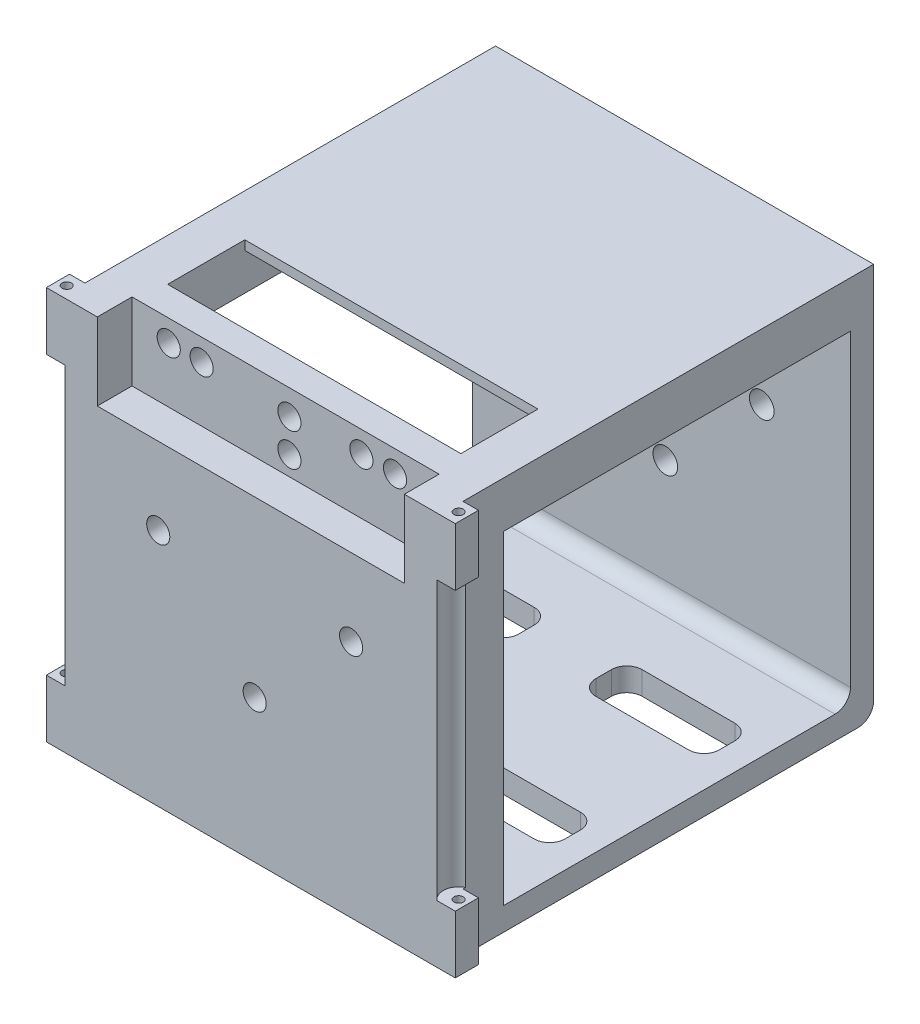
SolidWorks part; units mm, degrees
ref_plane "前视基准面" through (0, 0, 0) normal (0, 0, 1) x (1, 0, 0)
ref_plane "上视基准面" through (0, 0, 0) normal (0, 1, 0) x (1, 0, 0)
ref_plane "右视基准面" through (0, 0, 0) normal (1, 0, 0) x (0, 0, -1)
sketch "草图1" plane through (0, 0, 0) normal (0, 0, 1) x (1, 0, 0)
  line L0 (-0.5, 20) -> (-0.5, -31) construction
  line L2 (-25, 20) -> (-25, -31)
  line L3 (-25, -31) -> (24, -31)
  line L4 (24, 20) -> (24, -31)
  line L5 (-25, 0) -> (24, 0) construction
  line L13 (-25, 20) -> (24, 20)
  circle A0 centre (0, 0) radius 6
  circle A1 centre (12.5, 0) radius 1.6
  circle A2 centre (-12.5, 0) radius 1.6
  circle A3 centre (0, 12.5) radius 1.6
  circle A4 centre (0, -12.5) radius 1.6
  point P0 (0, 0)
  dimension "D3" = 3.2
  dimension "D5" = 3.2
  dimension "D6" = 3.2
  dimension "D8" = 12
  dimension "D7" = 3.2
  dimension "D2" = 25
  dimension "D4" = 25
  dimension "D9" = 49
  dimension "D10" = 51
extrude "凸台-拉伸1" add sketch "草图1" along normal blind 3
sketch "草图2" plane through (0, -31, 0) normal (0, -1, 0) x (1, 0, 0)
  line L0 (-25, 3) -> (-25, 48)
  line L1 (-25, 48) -> (24, 48)
  line L2 (24, 48) -> (24, 3)
  line L3 (-0.5, 48) -> (-0.5, 3) construction
  line L4 (-25, 25.5) -> (-0.5, 25.5) construction
  line L5 (-0.5, 25.5) -> (24, 25.5) construction
  line L6 (-25, 3) -> (24, 3) construction
  line L7 (-25, 3) -> (24, 3)
  line L8 (-21.5, 18.5) -> (-5.5, 18.5)
  line L9 (-21.5, 18.5) -> (-21.5, 12.5)
  line L10 (-21.5, 12.5) -> (-5.5, 12.5)
  line L11 (-5.5, 18.5) -> (-5.5, 12.5)
  line L12 (-21.5, 18.5) -> (-5.5, 12.5) construction
  line L13 (-21.5, 12.5) -> (-5.5, 18.5) construction
  line L14 (4.5, 18.5) -> (4.5, 12.5)
  line L15 (20.5, 12.5) -> (4.5, 12.5)
  line L16 (20.5, 18.5) -> (20.5, 12.5)
  line L17 (20.5, 18.5) -> (4.5, 18.5)
  line L18 (-21.5, 32.5) -> (-21.5, 38.5)
  line L19 (-5.5, 32.5) -> (-5.5, 38.5)
  line L20 (-21.5, 38.5) -> (-5.5, 38.5)
  line L21 (-21.5, 32.5) -> (-5.5, 32.5)
  line L22 (20.5, 32.5) -> (20.5, 38.5)
  line L23 (20.5, 38.5) -> (4.5, 38.5)
  line L24 (4.5, 32.5) -> (4.5, 38.5)
  line L25 (20.5, 32.5) -> (4.5, 32.5)
  point P20 (-13.5, 15.5)
  dimension "D1" = 45
  dimension "D2" = 49
  dimension "D3" = 16
  dimension "D4" = 6
  dimension "D5" = 10
  dimension "D6" = 13
extrude "凸台-拉伸2" add sketch "草图2" against normal blind 3
sketch "草图3" plane through (0, 0, 48) normal (0, 0, 1) x (1, 0, 0)
  line L0 (24, 20) -> (-25, 20)
  line L1 (-25, -31) -> (24, -31)
  line L2 (-25, -31) -> (-25, 20)
  line L4 (24, -31) -> (24, 20)
  line L5 (24, -28) -> (-25, -28) construction
  circle A1 centre (-12.5, 0) radius 1.5
  circle A2 centre (12.5, 0) radius 1.5
  circle A3 centre (0, -12.5) radius 1.5
  circle A4 centre (0, 12.5) radius 1.5
  circle A5 centre (0, 16.75) radius 1.5
  dimension "D1" = 3
  dimension "D2" = 3
  dimension "D3" = 3
  dimension "D4" = 3
  dimension "D5" = 4.25
  dimension "D7" = 3
  dimension "D6" = 48
  dimension "D8" = 49
extrude "凸台-拉伸3" add sketch "草图3" along normal blind 8.22
fillet "圆角2" radius 2 1 edges at (-5.5, -29.5, 12.5)
fillet "圆角3" radius 2 3 edges at (-21.5, -29.5, 18.5) (-21.5, -29.5, 12.5) (-5.5, -29.5, 18.5)
fillet "圆角4" radius 2 12 edges at (-21.5, -29.5, 32.5) (-21.5, -29.5, 38.5) (-5.5, -29.5, 32.5) (-5.5, -29.5, 38.5) (4.5, -29.5, 38.5) (4.5, -29.5, 32.5) (20.5, -29.5, 38.5) (20.5, -29.5, 32.5) (4.5, -29.5, 18.5) (20.5, -29.5, 18.5) (20.5, -29.5, 12.5) (4.5, -29.5, 12.5)
fillet "圆角5" radius 2 1 edges at (-0.5, -28, 3)
fillet "圆角6" radius 2 1 edges at (-0.5, -31, 0)
ref_plane "基准面1" through (0, -31, 0) normal (0, -1, 0) x (-1, 0, 0)
sketch "草图4" plane through (0, -31, 0) normal (0, -1, 0) x (-1, 0, 0)
  line L0 (-24, -56.22) -> (-26, -56.22)
  line L1 (-26, -56.22) -> (-26, -53.22)
  line L2 (-26, -53.22) -> (-24, -53.22)
  line L3 (-24, -56.22) -> (-24, -2) construction
  line L4 (-24, -53.22) -> (-24, -56.22)
  line L5 (0.5, -56.22) -> (0.5, -41.9466) construction
  line L6 (25, -56.22) -> (-24, -56.22) construction
  line L7 (25, -53.22) -> (25, -56.22)
  line L8 (25, -56.22) -> (27, -56.22)
  line L9 (27, -56.22) -> (27, -53.22)
  line L10 (27, -53.22) -> (25, -53.22)
  dimension "D1" = 3
  dimension "D2" = 2
extrude "凸台-拉伸4" add sketch "草图4" against normal blind 51
ref_plane "基准面2" through (0, 20, 0) normal (0, 1, 0) x (1, 0, 0)
sketch "草图5" plane through (0, 20, 0) normal (0, 1, 0) x (1, 0, 0)
  line L0 (-25, -48) -> (-19.5, -48)
  line L1 (24, -48) -> (-25, -48) construction
  line L2 (-19.5, -48) -> (-19.5, -2.9625)
  line L3 (-19.5, -2.9625) -> (-25, -2.9625)
  line L4 (-25, -3) -> (-25, 0) construction
  line L5 (-25, -2.9625) -> (-25, -48)
  line L7 (-0.5, -48) -> (-0.5, -40.8313) construction
  line L8 (24, -48) -> (-25, -48) construction
  line L10 (18.5, -2.9625) -> (24, -2.9625)
  line L11 (18.5, -48) -> (18.5, -2.9625)
  line L12 (24, -48) -> (18.5, -48)
  line L13 (24, -2.9625) -> (24, -48)
  dimension "D1" = 5.5
extrude "凸台-拉伸5" add sketch "草图5" against normal blind 6
hole_wizard "大小mm 暗销孔3" positions "草图10" profile "草图11" hole size "Ø3.0" standard "ISO" end condition up to next
sketch "草图10" plane through (0, 0, 48) normal (0, 0, -1) x (-1, 0, 0)
  point P0 (15.6437, 17.1723)
  point P2 (11.3773, 17.1723)
  point P4 (-13.687, 17.1723)
  point P6 (-9.3327, 17.1723)
sketch "草图11" plane through (-15.6437, 17.1723, 48) normal (1, 0, 0) x (0, 1, 0)
  line L0 (0, 0) -> (0, 8.22)
  line L1 (0, 8.22) -> (1.5, 8.22)
  line L2 (1.5, 8.22) -> (1.5, 0)
  line L5 (1.5, 0) -> (0, 0)
  line L11 (0, -6.35) -> (0, 107.95) construction
  dimension "通孔孔直径" = 3
  dimension "通孔孔深度" = 8.22
sketch "草图12" plane through (0, 20, 0) normal (0, 1, 0) x (1, 0, 0)
  line L0 (-20.4, -56.22) -> (-20.4, -51.72)
  line L1 (26, -56.22) -> (-27, -56.22) construction
  line L2 (-20.4, -51.72) -> (19.4, -51.72)
  line L3 (19.4, -51.72) -> (19.4, -56.22)
  line L4 (-19.5, -48) -> (-19.5, -3) construction
  line L5 (18.5, -3) -> (18.5, -48) construction
  line L6 (-20.4, -56.22) -> (19.4, -56.22)
  dimension "D1" = 4.5
  dimension "D2" = 0.9
  dimension "D3" = 0.9
extrude "切除-拉伸6" cut sketch "草图12" against normal blind 10
sketch "草图13" plane through (0, 0, 0) normal (0, 0, -1) x (-1, 0, 0)
  line L0 (-26, -23.5) -> (-26, 12.5)
  line L1 (-26, 20) -> (-26, -31) construction
  line L2 (-26, 12.5) -> (-24, 12.5)
  line L3 (-24, -29) -> (-24, 20) construction
  line L4 (-24, 12.5) -> (-24, -23.5)
  line L5 (-24, 20) -> (-24, -31) construction
  line L6 (-26, -5.5) -> (25, -5.5) construction
  line L7 (25, 20) -> (25, -31) construction
  line L8 (-26, -23.5) -> (-24, -23.5)
  line L9 (0.5, 20) -> (0.5, -31) construction
  line L10 (-24, 20) -> (25, 20) construction
  line L11 (25, -31) -> (-24, -31) construction
  line L12 (27, -23.5) -> (25, -23.5)
  line L13 (27, -23.5) -> (27, 12.5)
  line L14 (25, 12.5) -> (25, -23.5)
  line L15 (27, 12.5) -> (25, 12.5)
  point P14 (-24, -5.5)
  dimension "D1" = 18
extrude "切除-拉伸7" cut sketch "草图13" against normal through all
sketch "草图14" plane through (0, 20, 0) normal (0, 1, 0) x (1, 0, 0)
  line L0 (-0.5, -56.22) -> (-0.5, 0) construction
  line L1 (-20.4, -56.22) -> (19.4, -56.22) construction
  line L2 (24, 0) -> (-25, 0) construction
  line L4 (26, -53.22) -> (26, -56.22) construction
  circle A0 centre (24.9, -54.6865) radius 1.5 construction
  circle A1 centre (-25.9, -54.6865) radius 1.5 construction
  circle A2 centre (24.9, -54.6865) radius 0.6
  circle A3 centre (-25.9, -54.6865) radius 0.6
  dimension "D1" = 3
  dimension "D3" = 1.2
  dimension "D2" = 1.1
extrude "切除-拉伸8" cut sketch "草图14" against normal through all
sketch "草图15" plane through (0, 12.5, 0) normal (0, -1, 0) x (1, 0, 0)
  line L0 (-0.5, 56.22) -> (-0.5, 0) construction
  line L1 (-27, 56.22) -> (26, 56.22) construction
  line L2 (24, 0) -> (-25, 0) construction
  circle A0 centre (24.9, 54.6865) radius 2
  circle A1 centre (-25.9, 54.6865) radius 2
  dimension "D1" = 4
extrude "切除-拉伸9" cut sketch "草图15" along normal up to surface (36 mm away) up to face at (25.5, -23.5, 54.6865)
sketch "草图16" plane through (0, 0, 3) normal (0, 0, 1) x (1, 0, 0)
  line L0 (18.5, 20) -> (18.5, 14) construction
  line L1 (-19.5, 20) -> (18.5, 20)
  line L2 (-19.5, 20) -> (-19.5, 18.8)
  line L3 (-19.5, 18.8) -> (18.5, 18.8)
  line L4 (18.5, 20) -> (18.5, 18.8)
  dimension "D1" = 1.2
extrude "凸台-拉伸6" add sketch "草图16" along normal blind 35
